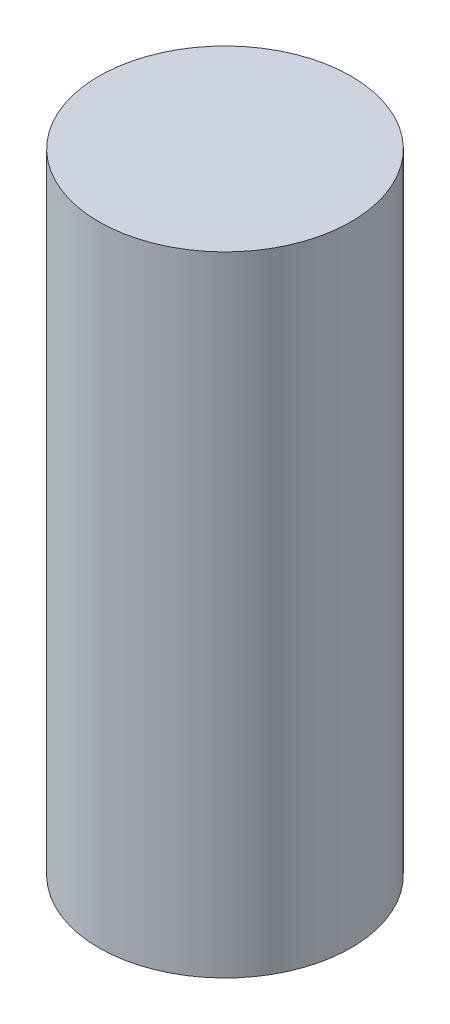
SolidWorks part; units mm, degrees
ref_plane "Front Plane" through (0, 0, 0) normal (0, 0, 1) x (1, 0, 0)
ref_plane "Top Plane" through (0, 0, 0) normal (0, 1, 0) x (1, 0, 0)
ref_plane "Right Plane" through (0, 0, 0) normal (1, 0, 0) x (0, 0, -1)
sketch "Sketch2" plane through (0, 0, 0) normal (0, 1, 0) x (1, 0, 0)
  circle A0 centre (0, 0) radius 3.1051
  dimension "D1" = 6.2103
extrude "Boss-Extrude1" add sketch "Sketch2" along normal blind 15.4813
